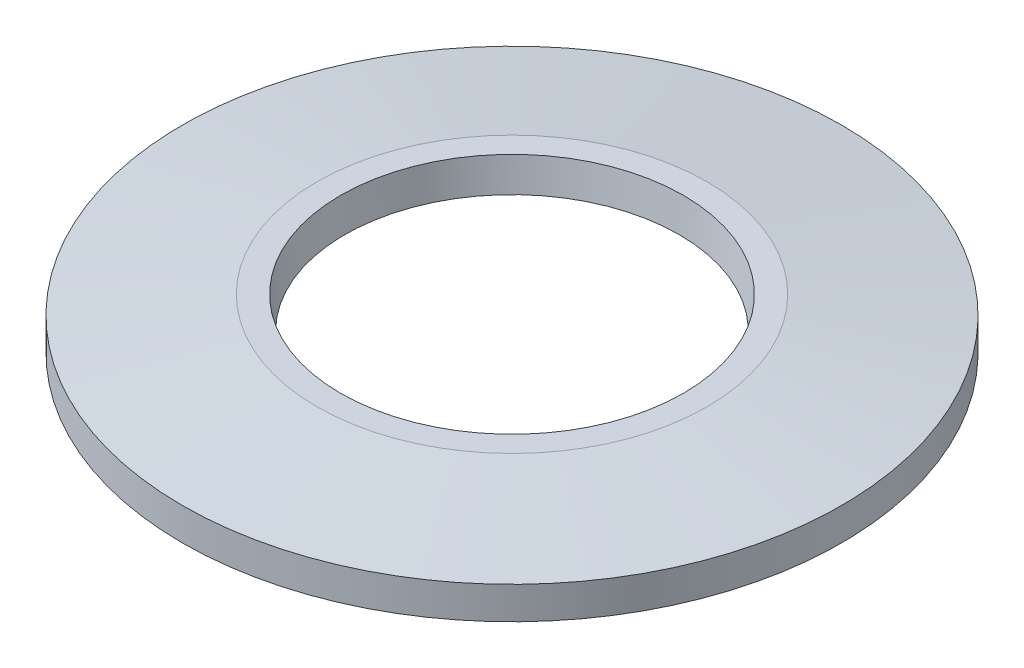
SolidWorks part; units mm, degrees
material "Cast Alloy Steel"
ref_plane "Front Plane" through (0, 0, 0) normal (0, 0, 1) x (1, 0, 0)
ref_plane "Top Plane" through (0, 0, 0) normal (0, 1, 0) x (1, 0, 0)
ref_plane "Right Plane" through (0, 0, 0) normal (1, 0, 0) x (0, 0, -1)
sketch "Sketch1" plane through (0, 0, 0) normal (1, 0, 0) x (0, 0, -1)
  line L0 (0, -9.2952) -> (0, 21.6016) construction
  line L1 (-14, -2.15) -> (-13, -2.15)
  line L2 (-13, -2.15) -> (-7.1, -1.354)
  line L3 (-7.1, -1.354) -> (-7.2827, 0)
  line L4 (-7.2827, 0) -> (-8.2827, 0)
  line L5 (-8.2827, 0) -> (-14, -0.7713)
  line L6 (-14, -0.7713) -> (-14, -2.15)
  dimension "D1" = 1.5
  dimension "D2" = 2.15
  dimension "D3" = 7.1
  dimension "D4" = 14
  dimension "D5" = 1
revolve "Revolve1" add sketch "Sketch1" angle 360 about L0
